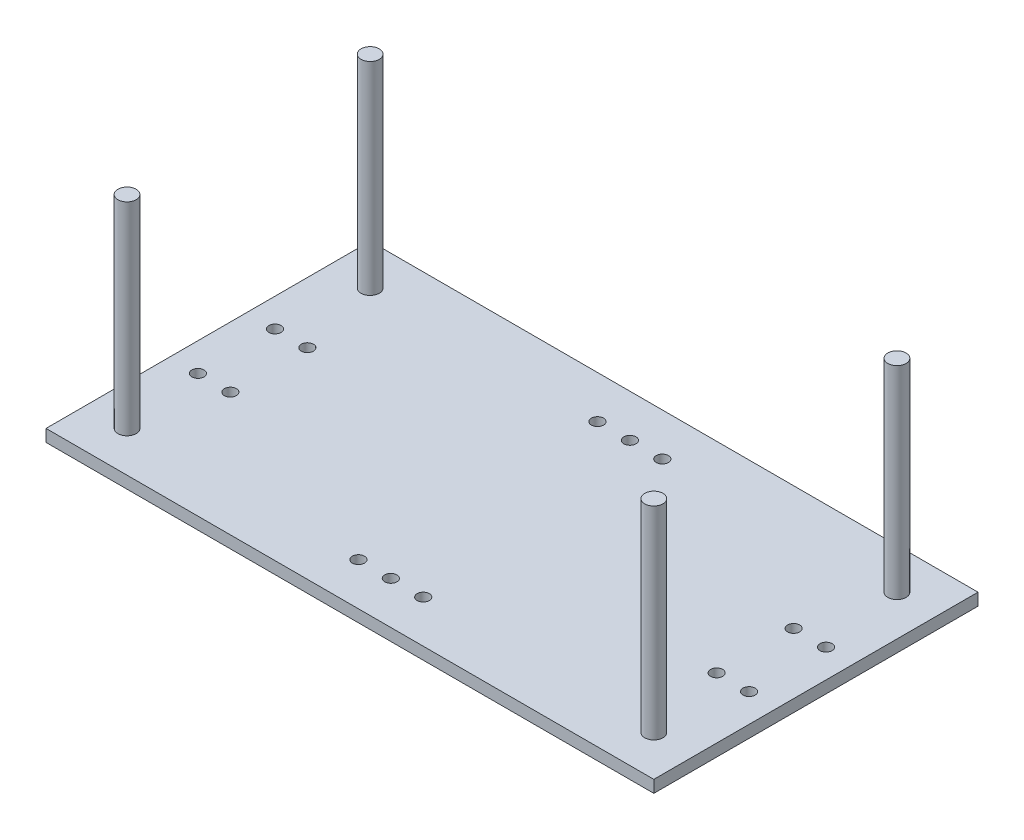
SolidWorks part; units mm, degrees
ref_plane "Front Plane" through (0, 0, 0) normal (0, 0, 1) x (1, 0, 0)
ref_plane "Top Plane" through (0, 0, 0) normal (0, 1, 0) x (1, 0, 0)
ref_plane "Right Plane" through (0, 0, 0) normal (1, 0, 0) x (0, 0, -1)
sketch "Sketch2" plane through (0, 0, 0) normal (0, 1, 0) x (1, 0, 0)
  line L0 (-83.4647, 1.8257) -> (66.5353, 1.8257)
  line L1 (-83.4647, 41.8257) -> (66.5353, 41.8257)
  line L2 (-83.4647, 41.8257) -> (-83.4647, -38.1743)
  line L3 (-83.4647, -38.1743) -> (66.5353, -38.1743)
  line L4 (66.5353, 41.8257) -> (66.5353, -38.1743)
  circle A0 centre (-68.4647, 11.3257) radius 1.5
  circle A1 centre (-68.4647, -7.6743) radius 1.5
  circle A2 centre (-76.4647, 11.3257) radius 1.5
  circle A3 centre (-76.4647, -7.6743) radius 1.5
  circle A4 centre (51.5353, -7.6743) radius 1.5
  circle A5 centre (59.5353, -7.6743) radius 1.5
  circle A6 centre (59.5353, 11.3257) radius 1.5
  circle A7 centre (51.5353, 11.3257) radius 1.5
  dimension "D3" = 3
  dimension "D7" = 3
  dimension "D1" = 80
  dimension "D2" = 150
  dimension "D4" = 19
  dimension "D5" = 15
  dimension "D6" = 9.5
  dimension "D8" = 7
  dimension "D9" = 7
  dimension "D10" = 15
extrude "Boss-Extrude1" add sketch "Sketch2" against normal blind 3 contours L4 L0 L2 L3 A3 A1 | L4 L1 L2 L0 A2 A0
sketch "Sketch3" plane through (0, 0, 0) normal (0, 1, 0) x (1, 0, 0)
  line L0 (-83.4647, 41.8257) -> (-83.4647, -38.1743) construction
  line L1 (-83.4647, 41.8257) -> (66.5353, 41.8257) construction
  line L2 (-83.4647, -38.1743) -> (66.5353, -38.1743) construction
  line L3 (66.5353, 41.8257) -> (66.5353, -38.1743) construction
  circle A4 centre (56.5353, 31.8257) radius 2.25
  circle A5 centre (56.5353, -28.1743) radius 2.25
  circle A6 centre (-73.4647, -28.1743) radius 2.25
  circle A7 centre (-73.4647, 31.8257) radius 2.25
  dimension "D11" = 4.5
  dimension "D12" = 4.5
  dimension "D13" = 4.5
  dimension "D2" = 10
  dimension "D3" = 10
  dimension "D4" = 10
  dimension "D5" = 10
  dimension "D6" = 10
  dimension "D7" = 10
  dimension "D8" = 10
  dimension "D9" = 10
extrude "Boss-Extrude2" add sketch "Sketch3" along normal blind 50
sketch "Sketch4" plane through (0, -3, 0) normal (0, -1, 0) x (-1, 0, 0)
  circle A0 centre (16.8674, 31.3257) radius 1.5
  circle A1 centre (8.8674, 31.3257) radius 1.5
  circle A2 centre (0.8674, 31.3257) radius 1.5
  circle A3 centre (16.8674, -27.6743) radius 1.5
  circle A4 centre (8.8674, -27.6743) radius 1.5
  circle A5 centre (0.8674, -27.6743) radius 1.5
extrude "Cut-Extrude1" cut sketch "Sketch4" against normal blind 10
